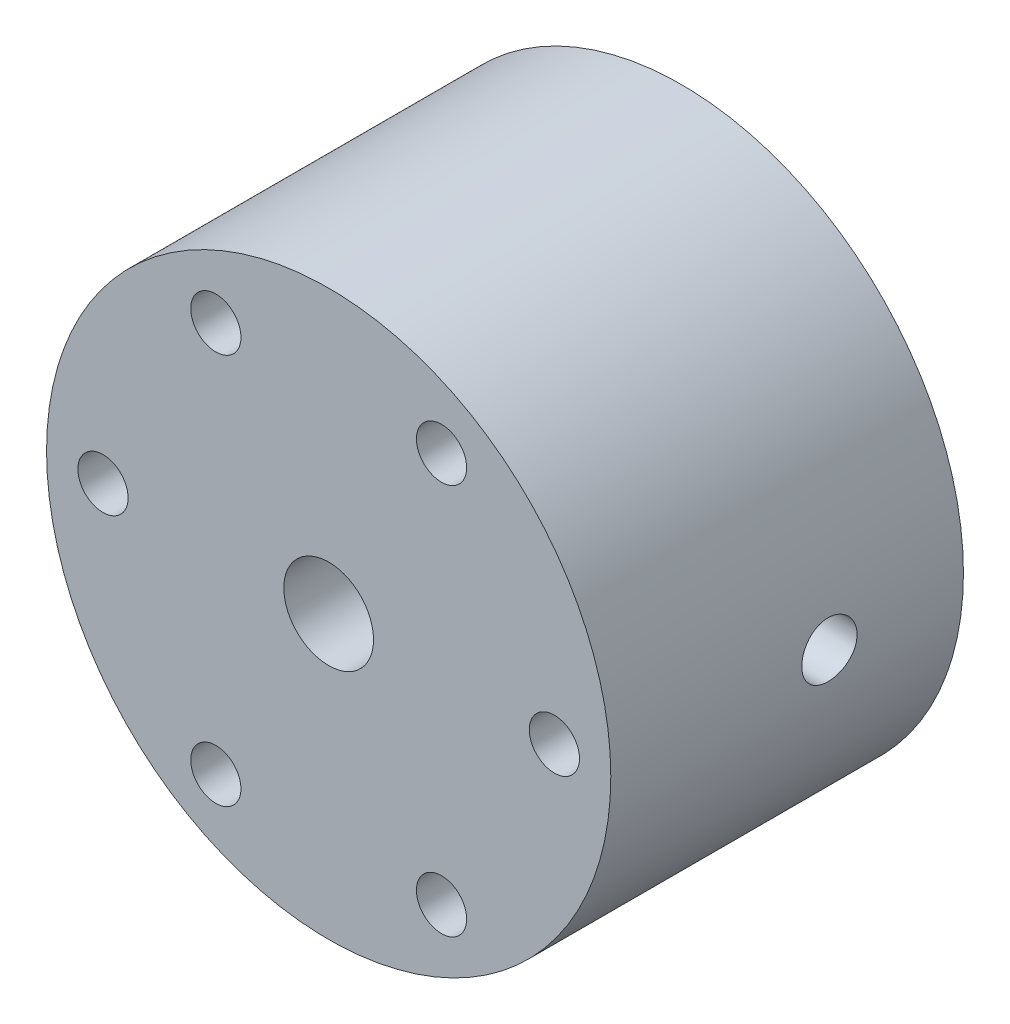
SolidWorks part; units mm, degrees
other "DetailItem1"
ref_plane "Front Plane" through (0, 0, 0) normal (0, 0, 1) x (1, 0, 0)
ref_plane "Top Plane" through (0, 0, 0) normal (0, 1, 0) x (1, 0, 0)
ref_plane "Right Plane" through (0, 0, 0) normal (1, 0, 0) x (0, 0, -1)
sketch "Sketch1" plane through (0, 0, 0) normal (0, 0, 1) x (1, 0, 0)
  circle A0 centre (0, 0) radius 12.7
  dimension "D1" = 25.4
extrude "Boss-Extrude1" add sketch "Sketch1" against normal blind 15.875
shell "Shell1" thickness 6.35
ref_plane "Plane1" through (0, 0, -9.8425) normal (0, 0, -1) x (-1, 0, 0)
sketch "Sketch3" plane through (0, 0, -9.8425) normal (0, 0, -1) x (-1, 0, 0)
  line L0 (12.7, 0) -> (-12.7, 0) construction
  circle A0 centre (0, 0) radius 12.7 construction
sketch "Sketch4" plane through (0, 0, 0) normal (1, 0, 0) x (0, 0, -1)
  line L0 (9.8425, -13.97) -> (9.8425, 13.97) construction
  circle A0 centre (9.8425, 0) radius 1.2446
  dimension "D1" = 2.4892
extrude "Cut-Extrude1" cut sketch "Sketch4" against normal through all both and the other way through all
ref_plane "Plane2" through (0, 0, -14.605) normal (0, 0, -1) x (-1, 0, 0)
sketch "Sketch7" plane through (0, 0, -14.605) normal (0, 0, -1) x (-1, 0, 0)
  circle A0 centre (0, 0) radius 7.6962
  circle A1 centre (0, 0) radius 6.35 construction
  circle A2 centre (0, 0) radius 6.35
  dimension "D1" = 15.3924
extrude "Cut-Extrude2" cut sketch "Sketch7" against normal blind 2.3622
ref_plane "Oring Center" through (0, 0, -13.4239) normal (0, 0, -1) x (-1, 0, 0)
hole_wizard "Tap Drill for #10-32 Tap1" positions "Sketch11" profile "Sketch12" hole size "#10-32" standard "ANSI Inch" end condition through all
sketch "Sketch11" plane through (0, 0, 0) normal (0, 0, 1) x (1, 0, 0)
  point P0 (0, 0)
sketch "Sketch12" plane through (0, 0, 0) normal (1, 0, 0) x (0, -1, 0)
  line L0 (0, 0) -> (0, 15.875)
  line L1 (0, 15.875) -> (2.0193, 15.875)
  line L2 (2.0193, 15.875) -> (2.0193, 0)
  line L5 (2.0193, 0) -> (0, 0)
  line L11 (0, -6.35) -> (0, 107.95) construction
  dimension "Thru Hole Dia." = 4.0386
  dimension "Thru Hole Depth" = 15.875
sketch "Sketch13" plane through (0, 0, 0) normal (0, 0, 1) x (1, 0, 0)
  line L0 (0, 0) -> (-10.16, 0) construction
  point P4 (-10.16, 0)
  dimension "D1" = 10.16
hole_wizard "Tap Drill for #4-40 Tap1" positions "Sketch14" profile "Sketch15" hole size "#4-40" standard "ANSI Inch"
sketch "Sketch14" plane through (0, 0, 0) normal (0, 0, 1) x (1, 0, 0)
  point P0 (-10.16, 0)
sketch "Sketch15" plane through (-10.16, 0, 0) normal (1, 0, 0) x (0, -1, 0)
  line L0 (0, 0) -> (0, 5.7592)
  line L1 (0, 5.7592) -> (1.1303, 5.08)
  line L2 (1.1303, 5.08) -> (1.1303, 0)
  line L5 (1.1303, 0) -> (0, 0)
  line L10 (0, 5.7592) -> (-1.1303, 5.08) construction
  line L11 (0, -6.35) -> (0, 107.95) construction
  dimension "Hole Dia." = 2.2606
  dimension "Hole Depth" = 5.08
  dimension "Drill Angle" = 118
pattern_circular "CirPattern1" count 6 over 360 about axis through (0, 0, 0) along (0, 0, 1) of "Tap Drill for #4-40 Tap1"
